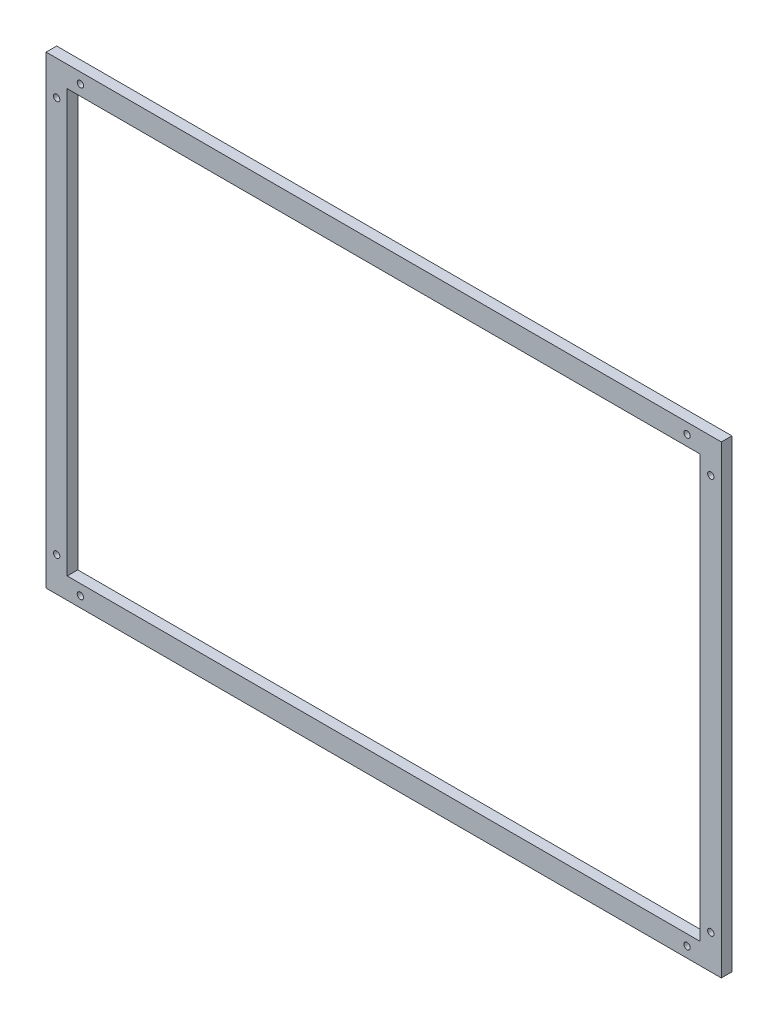
SolidWorks part; units mm, degrees
ref_plane "Plan de face" through (0, 0, 0) normal (0, 0, 1) x (1, 0, 0)
ref_plane "Plan de dessus" through (0, 0, 0) normal (0, 1, 0) x (1, 0, 0)
ref_plane "Plan de droite" through (0, 0, 0) normal (1, 0, 0) x (0, 0, -1)
sketch "Esquisse1" plane through (0, 0, 0) normal (0, 0, 1) x (1, 0, 0)
  line L1 (0, 0) -> (-640, 0)
  line L2 (0, 0) -> (0, 440)
  line L3 (0, 440) -> (-640, 440)
  line L4 (-640, 0) -> (-640, 440)
  line L5 (-620, 420) -> (-20, 420)
  line L6 (-620, 420) -> (-620, 20)
  line L7 (-620, 20) -> (-20, 20)
  line L8 (-20, 420) -> (-20, 20)
  dimension "D1" = 640
  dimension "D2" = 440
  dimension "D3" = 20
  dimension "D4" = 20
  dimension "D5" = 20
  dimension "D6" = 20
extrude "Boss.-Extru.1" add sketch "Esquisse1" along normal blind 10
sketch "Esquisse2" plane through (0, 0, 10) normal (0, 0, 1) x (1, 0, 0)
  line L0 (0, 0) -> (0, 440) construction
  line L1 (0, 440) -> (-640, 440) construction
  line L2 (-20, 420) -> (-620, 420) construction
  line L3 (-640, 0) -> (0, 0) construction
  line L4 (-620, 20) -> (-20, 20) construction
  line L5 (-640, 440) -> (-640, 0) construction
  line L6 (-620, 420) -> (-620, 20) construction
  circle A0 centre (-32.5, 430) radius 3
  circle A1 centre (-10, 407.5) radius 3
  circle A2 centre (-607.5, 430) radius 3
  circle A3 centre (-630, 407.5) radius 3
  circle A4 centre (-630, 32.5) radius 3
  circle A5 centre (-607.5, 10) radius 3
  circle A6 centre (-32.5, 10) radius 3
  circle A7 centre (-10, 32.5) radius 3
  dimension "D1" = 6
  dimension "D2" = 6
  dimension "D3" = 32.5
  dimension "D4" = 32.5
  dimension "D5" = 10
  dimension "D6" = 10
  dimension "D7" = 6
  dimension "D8" = 6
  dimension "D9" = 32.5
  dimension "D10" = 32.5
  dimension "D11" = 10
  dimension "D12" = 10
  dimension "D13" = 6
  dimension "D14" = 32.5
  dimension "D15" = 32.5
  dimension "D16" = 6
  dimension "D17" = 10
  dimension "D18" = 10
  dimension "D19" = 6
  dimension "D20" = 6
  dimension "D21" = 10
  dimension "D22" = 10
  dimension "D23" = 32.5
  dimension "D24" = 32.5
extrude "Enlèv. mat.-Extru.1" cut sketch "Esquisse2" against normal through all
